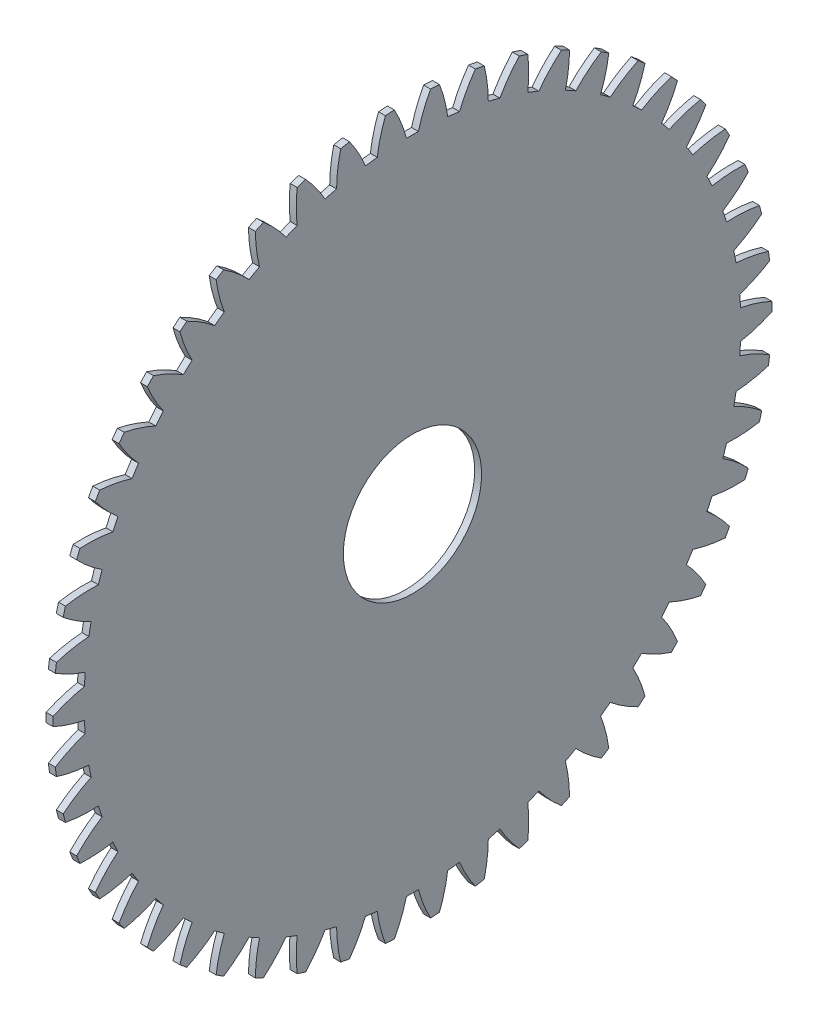
SolidWorks part; units mm, degrees
ref_plane "Plane1" through (0, 0, 0) normal (0, 0, 1) x (1, 0, 0)
ref_plane "Plane2" through (0, 0, 0) normal (0, 1, 0) x (1, 0, 0)
ref_plane "Plane3" through (0, 0, 0) normal (1, 0, 0) x (0, 0, -1)
other "Configuration Table"
sketch "HoldingSke" plane through (0, 0, 0) normal (0, 1, 0) x (1, 0, 0)
  line L0 (0, 0) -> (0.1071, -0.1277)
  line L1 (-15, 0) -> (100, 0) construction
  line L2 (0, 0) -> (-2.1039, 2.3779)
  line L3 (0, 0) -> (-11.863, 4.5341)
  line L4 (0, 0) -> (5.5511, 6.6156)
  line L5 (0, 0) -> (-46.8476, -17.4728)
  line L6 (0, 0) -> (-2.4869, -1.6779)
  line L7 (-2.1039, 2.3779) -> (8.6586, 51.2059)
  line L8 (-76.2, 54.61) -> (-71.8, 54.61)
  line L9 (-71.009, 38.7566) -> (-53.1078, 45.2721)
  line L10 (-76.2, 71.12) -> (104.1128, 71.12)
  line L11 (0, 0) -> (-3, 0)
  line L12 (-76.2, 101.6) -> (-75.993, 101.6)
  line L13 (24.9733, 27.94) -> (52.9518, 28.4284)
  line L14 (24.9733, 27.94) -> (24.9743, 27.94)
  line L15 (24.9733, 27.94) -> (100.4006, 29.5858)
  line L16 (-63.627, -6) -> (-12.827, -6)
  circle A0 centre (0, 0) radius 30
  circle A1 centre (0, 0) radius 37.5
  circle A2 centre (0, 0) radius 37.5
  circle A3 centre (0, 0) radius 30
  dimension "MHD" = 75
  dimension "Hub_dia" = 75
  dimension "Bore" = 60
  dimension "MBD" = 60
  dimension "Num_teeth" = 50
  dimension "Pitch" = 0.1667
  dimension "Overall_len" = 50
  dimension "Show_teeth" = 50
  dimension "Thickness" = 3
  dimension "OAL" = 50.0001
  dimension "T_dim" = 4.4
  dimension "Ap" = 20
  dimension "H" = 19.05
  dimension "Pitch_radius" = 180.3128
  dimension "Width" = 3
  dimension "Backlash" = 0.207
  dimension "Addendum_fac" = 1
  dimension "Dedendum_fac" = 1.25
  dimension "Clearance_fac" = 0.25
  dimension "Dedendum_add" = 0.001
  dimension "Module" = 6
sketch "BasProSke" plane through (0, 0, 0) normal (0, 1, 0) x (1, 0, 0)
  line L0 (-10, 0) -> (60, 0) construction
  line L1 (0, 0) -> (0, 156)
  line L2 (0, 0) -> (3, 0)
  line L3 (3, 0) -> (3, 156)
  line L4 (3, 156) -> (0, 156)
  dimension "Thickness" = 3
  dimension "Diameter" = 312
revolve "Base-Revolve" add sketch "BasProSke" angle 360 about L0
sketch "TooCutSke" plane through (0, 0, 0) normal (1, 0, 0) x (0, 0, -1)
  line L1 (0, 0) -> (0, 107) construction
  line L2 (0, 0) -> (-5.0738, 149.9142) construction
  line L3 (0, 0) -> (-18.8292, 299.2821) construction
  line L4 (-5.0738, 149.9142) -> (-9.4146, 149.6411) construction
  arc A0 (2.5924, 142.4754) -> (-2.5924, 142.4754) centre (0, 0) ccw
  arc A1 (7.8712, 155.8267) -> (-7.8712, 155.8267) centre (0, 0) ccw
  circle A2 centre (0, 0) radius 150 construction
  circle A3 centre (0, 0) radius 140.9539 construction
  arc A4 (-2.5924, 142.4754) -> (-7.8712, 155.8267) centre (-60.6281, 127.2487) ccw
  arc A5 (7.8712, 155.8267) -> (2.5924, 142.4754) centre (60.6281, 127.2487) ccw
  dimension "Root_dia" = 284.998
  dimension "Overcut_dia" = 312.0508
  dimension "Pitch_dia" = 300
  dimension "Base_dia" = 281.9078
  dimension "Flank_rad" = 60
  dimension "Half_ang" = 3.6
  dimension "Half_CT" = 4.3494
extrude "ToothCut" cut sketch "TooCutSke" along normal through all
fillet "Breaks" [suppressed] radius 0.12
fillet "RootFillets" [suppressed] radius 1.501
pattern_circular "TeethCuts" count 50 every 7.2 about axis through (-10, 0, 0) along (1, 0, 0) of "ToothCut", "RootFillets", "Breaks"
sketch "HubNeaOneSke" plane through (0, 0, 0) normal (-1, 0, 0) x (0, 0, 1)
  circle A0 centre (0, 0) radius 37.5
  dimension "Diameter" = 75
extrude "HubNearOne" [suppressed] add sketch "HubNeaOneSke" along normal blind 47.0001
sketch "HubNeaBotSke" plane through (0, 0, 0) normal (-1, 0, 0) x (0, 0, 1)
  circle A0 centre (0, 0) radius 37.5
  dimension "Diameter" = 75
extrude "HubNearBoth" [suppressed] add sketch "HubNeaBotSke" along normal blind 23.5
ref_plane "FarPln" through (3, 0, 0) normal (1, 0, 0) x (0, 0, -1)
sketch "HubFarSke" plane through (3, 0, 0) normal (1, 0, 0) x (0, 0, -1)
  circle A0 centre (0, 0) radius 37.5
  dimension "Diameter" = 75
extrude "HubFar" [suppressed] add sketch "HubFarSke" along normal blind 23.5
sketch "BorSke" plane through (0, 0, 0) normal (1, 0, 0) x (0, 0, -1)
  circle A0 centre (0, 0) radius 30
  dimension "Diameter" = 60
extrude "Bore" cut sketch "BorSke" along normal mid plane 100.0001
sketch "KeySke" plane through (0, 0, 0) normal (1, 0, 0) x (0, 0, -1)
  line L0 (-9, 0) -> (-9, 34.4)
  line L1 (-9, 34.4) -> (9, 34.4)
  line L2 (9, 34.4) -> (9, 0)
  line L3 (0, 0) -> (0, 34) construction
  line L4 (-9, 0) -> (9, 0)
  dimension "Offset" = 34.4
  dimension "Width" = 18
extrude "Keyway" [suppressed] cut sketch "KeySke" along normal mid plane 100.0001
pattern_circular "Keyway2" [suppressed] count 2 every 90 about axis through (-10, 0, 0) along (1, 0, 0)
sketch "Sketch1" plane through (3, 0, 0) normal (1, 0, 0) x (0, 0, -1)
  circle A0 centre (0, 0) radius 156
  point P3 (0, 0)
equation "' \"Module@HoldingSke\" = 6.35"
equation "' \"Num_teeth@HoldingSke\" = 12"
equation "' \"Ap@HoldingSke\" =  20"
equation "' \"Ap@HoldingSke\" = 20"
equation "' \"Width@HoldingSke\" = 0.5 * 25.4"
equation "' \"Hub_dia@HoldingSke\"= 1 * 25.4"
equation "' \"Hub_dia@HoldingSke\" = 1 * 25.4"
equation "' \"Overall_len@HoldingSke\" = 1.0 * 25.4"
equation "' \"Bore@HoldingSke\" = 0.75 * 25.4"
equation "' \"T_dim@HoldingSke\" = 0.1 * 25.4"
equation "' \"Width@KeySke\" = 0.25 * 25.4"
equation "' \"Show_teeth@HoldingSke\" = 13"
equation "' \"Backlash@HoldingSke\" = 0.009 * 25.4"
equation "' \"Addendum_fac@HoldingSke\" = 1.0"
equation "' \"Dedendum_fac@HoldingSke\" = 1.25"
equation "' \"Dedendum_add@HoldingSke\" = 0.00005 * 25.4"
equation "' \"Clearance_fac@HoldingSke\" = 0.25"
equation "\"Pitch@HoldingSke\" = 1 / \"Module@HoldingSke\""
equation "\"Overcut_dia@TooCutSke\" = (\"Num_teeth@HoldingSke\" + 2 * \"Addendum_fac@HoldingSke\") / \"Pitch@HoldingSke\" + 0.002 * 25.4"
equation "\"Pitch_dia@TooCutSke\" = \"Num_teeth@HoldingSke\" / \"Pitch@HoldingSke\""
equation "\"Base_dia@TooCutSke\" = \"Num_teeth@HoldingSke\" / \"Pitch@HoldingSke\" * cos((\"Ap@HoldingSke\"  * 3.14159265 / 180))"
equation "\"Root_dia@TooCutSke\" = (\"Num_teeth@HoldingSke\" + 2) / \"Pitch@HoldingSke\" - 2 * (\"Addendum_fac@HoldingSke\" + \"Dedendum_fac@HoldingSke\") / \"Pitch@HoldingSke\" - \"Dedendum_add@HoldingSke\" * 2"
equation "\"Half_ang@TooCutSke\" = 180 / \"Num_teeth@HoldingSke\""
equation "\"Half_CT@TooCutSke\" = \"Num_teeth@HoldingSke\" / \"Pitch@HoldingSke\" * sin((3.14159265 / 2 / \"Num_teeth@HoldingSke\")) / 2 - 7 * \"Backlash@HoldingSke\" / 4"
equation "\"Flank_rad@TooCutSke\" = \"Num_teeth@HoldingSke\" / \"Pitch@HoldingSke\" / 5"
equation "\"Radius@RootFillets\" = \"Clearance_fac@HoldingSke\" / \"Pitch@HoldingSke\" + \"Dedendum_add@HoldingSke\""
equation "\"Break_rad@Breaks\" = 0.02 / \"Pitch@HoldingSke\""
equation "\"Thickness@HoldingSke\" = \"Width@HoldingSke\""
equation "\"OAL@HoldingSke\" = \"Thickness@HoldingSke\""
equation "\"MHD@HoldingSke\" = (\"Num_teeth@HoldingSke\" + 2) / \"Pitch@HoldingSke\" - 2 * (\"Addendum_fac@HoldingSke\" + \"Dedendum_fac@HoldingSke\")  / \"Pitch@HoldingSke\" - \"Dedendum_add@HoldingSke\" * 2"
equation "\"MBD@HoldingSke\" = (\"Num_teeth@HoldingSke\" + 2) / \"Pitch@HoldingSke\" - 2 * (\"Addendum_fac@HoldingSke\" + \"Dedendum_fac@HoldingSke\")  / \"Pitch@HoldingSke\" - \"Dedendum_add@HoldingSke\" * 2 - 0.002 * 25.4"
equation "\"MHD@HoldingSke\" = ((sgn( \"MHD@HoldingSke\" - \"Hub_dia@HoldingSke\" )-1)*( \"MHD@HoldingSke\" - \"Hub_dia@HoldingSke\" ))/-2+ \"Hub_dia@HoldingSke\""
equation "\"MBD@HoldingSke\" = ((sgn( \"MBD@HoldingSke\" - \"Bore@HoldingSke\" )-1)*( \"MBD@HoldingSke\" - \"Bore@HoldingSke\" ))/-2+ \"Bore@HoldingSke\""
equation "\"OAL@HoldingSke\" = ((sgn( \"OAL@HoldingSke\" - \"Overall_len@HoldingSke\" )+1)*( \"OAL@HoldingSke\" - \"Overall_len@HoldingSke\" ))/2 + \"Overall_len@HoldingSke\" + 0.000002 * 25.4"
equation "\"Num_teeth@TeethCuts\" = int( \"Show_teeth@HoldingSke\" ) + 1"
equation "\"Num_teeth@TeethCuts\" = ((sgn( \"Num_teeth@TeethCuts\" - \"Num_teeth@HoldingSke\" )-1)*( \"Num_teeth@TeethCuts\" - \"Num_teeth@HoldingSke\" ))/-2+ \"Num_teeth@HoldingSke\""
equation "\"Num_teeth@TeethCuts\" = ((sgn( \"Num_teeth@TeethCuts\" - 2.0)+1)*( \"Num_teeth@TeethCuts\" - 2.0))/2 +2.0"
equation "\"Angle@TeethCuts\" = 360.0 / \"Num_teeth@HoldingSke\""
equation "\"Diameter@BasProSke\" = (\"Num_teeth@HoldingSke\" + 2 * \"Addendum_fac@HoldingSke\") / \"Pitch@HoldingSke\""
equation "\"Thickness@BasProSke\"  = \"Thickness@HoldingSke\""
equation "' \"Fillet_rad@BasProSke\" =  \"Thickness@HoldingSke\" * 0.05"
equation "' \"Fillet_rad@BasProSke\" = \"Thickness@HoldingSke\" * 0.05"
equation "\"MHD@HoldingSke\" = ((sgn( \"MHD@HoldingSke\" - \"Root_dia@TooCutSke\" )-1)*( \"MHD@HoldingSke\" - \"Root_dia@TooCutSke\" ))/-2+ \"Root_dia@TooCutSke\""
equation "\"Diameter@HubNeaOneSke\" = \"MHD@HoldingSke\""
equation "\"Length@HubNearOne\" = \"OAL@HoldingSke\" - \"Thickness@BasProSke\""
equation "\"Diameter@HubNeaBotSke\" = \"MHD@HoldingSke\""
equation "\"Length@HubNearBoth\" = ( \"OAL@HoldingSke\" - \"Thickness@BasProSke\" ) / 2.0"
equation "\"Thickness@FarPln\" = \"Thickness@BasProSke\""
equation "\"Diameter@HubFarSke\" = \"MHD@HoldingSke\""
equation "\"Length@HubFar\" = ( \"OAL@HoldingSke\" - \"Thickness@BasProSke\" ) / 2.0"
equation "\"Diameter@BorSke\" = \"MBD@HoldingSke\""
equation "\"D1@Bore\" = \"OAL@HoldingSke\" * 2.0"
equation "\"D1@Keyway\" = \"OAL@HoldingSke\" * 2.0"
equation "\"Offset@KeySke\" = \"T_dim@HoldingSke\" + \"MBD@HoldingSke\" / 2.0"
